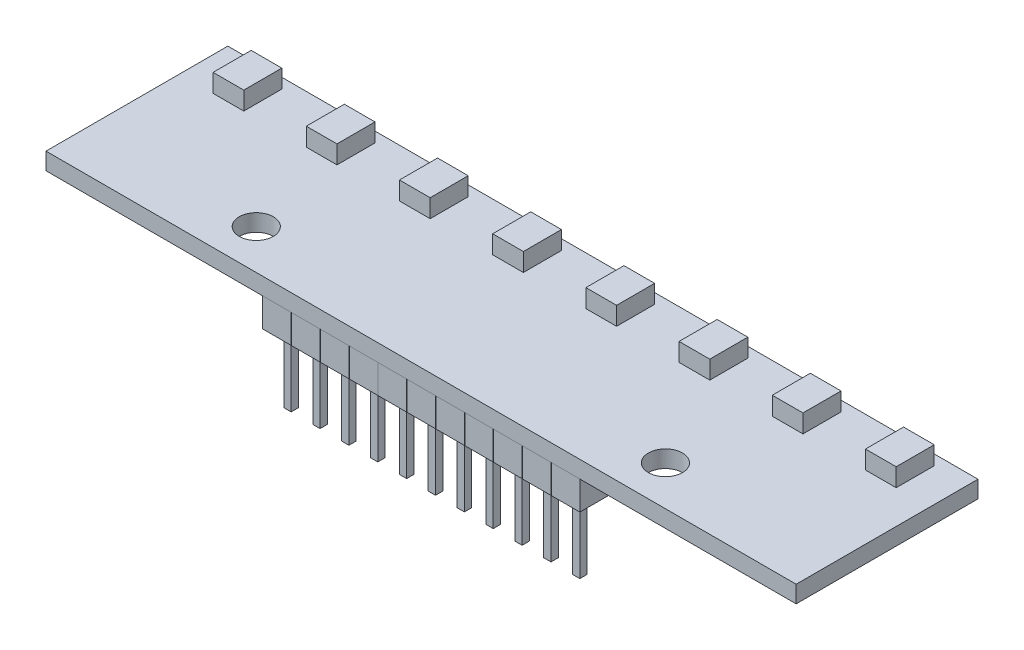
SolidWorks part; units mm, degrees
ref_plane "Front Plane" through (0, 0, 0) normal (0, 0, 1) x (1, 0, 0)
ref_plane "Top Plane" through (0, 0, 0) normal (0, 1, 0) x (1, 0, 0)
ref_plane "Right Plane" through (0, 0, 0) normal (1, 0, 0) x (0, 0, -1)
sketch "Sketch1" plane through (0, 0, 0) normal (0, 1, 0) x (1, 0, 0)
  line L0 (-18, -4.5) -> (18, -4.5) construction
  line L1 (-33, -8) -> (33, -8)
  line L2 (-33, -8) -> (-33, 8)
  line L3 (-33, 8) -> (33, 8)
  line L4 (33, -8) -> (33, 8)
  line L5 (-33, -8) -> (33, 8) construction
  line L6 (-33, 8) -> (33, -8) construction
  circle A0 centre (-18, -4.5) radius 1.5
  circle A1 centre (18, -4.5) radius 1.5
  point P0 (0, 0)
  point P10 (0, -4.5)
  dimension "D3" = 3
  dimension "D1" = 66
  dimension "D2" = 16
  dimension "D4" = 36
  dimension "D5" = 3.5
extrude "Boss-Extrude1" add sketch "Sketch1" against normal blind 1.5
sketch "Sketch2" plane through (0, -1.5, 0) normal (0, -1, 0) x (1, 0, 0)
  line L1 (-1.25, 7.98) -> (1.25, 7.98)
  line L3 (-1.25, 5.48) -> (1.25, 5.48)
  line L4 (1.25, 7.98) -> (1.25, 5.48)
  line L5 (-1.25, 7.98) -> (1.25, 5.48) construction
  line L6 (-1.25, 5.48) -> (1.25, 7.98) construction
  line L7 (-33, 8) -> (33, 8) construction
  line L11 (-1.25, 5.48) -> (-1.25, 7.98)
  point P4 (0, 6.73)
  point P6 (0, 5.48)
  dimension "D1" = 2.5
  dimension "D2" = 1.27
extrude "Boss-Extrude2" add sketch "Sketch2" along normal blind 2.54
sketch "Sketch3" plane through (0, -4.04, 0) normal (0, -1, 0) x (-1, 0, 0)
  line L0 (-1.25, -5.48) -> (-1.25, -7.98) construction
  line L1 (0.32, -6.41) -> (-0.32, -6.41)
  line L2 (0.32, -6.41) -> (0.32, -7.05)
  line L3 (0.32, -7.05) -> (-0.32, -7.05)
  line L4 (-0.32, -6.41) -> (-0.32, -7.05)
  line L5 (0.32, -6.41) -> (-0.32, -7.05) construction
  line L6 (0.32, -7.05) -> (-0.32, -6.41) construction
  point P0 (0, -6.73)
  point P10 (-1.25, -6.73)
  dimension "D1" = 0.64
extrude "Boss-Extrude3" add sketch "Sketch3" along normal blind 6
pattern_linear "LPattern1" count 6 spacing 2.54 along (-1, 0, 0) count 6 spacing 2.54 along (1, 0, 0) of "Boss-Extrude2", "Boss-Extrude3"
sketch "Sketch4" plane through (0, 0, 0) normal (0, 1, 0) x (1, 0, 0)
  line L0 (33, 8) -> (-33, 8) construction
  line L1 (-5.45, 7.1) -> (-2.75, 7.1)
  line L2 (-5.45, 7.1) -> (-5.45, 3.75)
  line L3 (-5.45, 3.75) -> (-2.75, 3.75)
  line L4 (-2.75, 7.1) -> (-2.75, 3.75)
  line L5 (2.75, 7.1) -> (5.45, 7.1)
  line L6 (2.75, 7.1) -> (2.75, 3.75)
  line L7 (2.75, 3.75) -> (5.45, 3.75)
  line L8 (5.45, 7.1) -> (5.45, 3.75)
  line L9 (10.95, 7.1) -> (13.65, 7.1)
  line L10 (10.95, 7.1) -> (10.95, 3.75)
  line L11 (10.95, 3.75) -> (13.65, 3.75)
  line L12 (13.65, 7.1) -> (13.65, 3.75)
  line L13 (19.15, 7.1) -> (21.85, 7.1)
  line L14 (19.15, 7.1) -> (19.15, 3.75)
  line L15 (19.15, 3.75) -> (21.85, 3.75)
  line L16 (21.85, 7.1) -> (21.85, 3.75)
  line L17 (27.35, 7.1) -> (30.05, 7.1)
  line L18 (27.35, 7.1) -> (27.35, 3.75)
  line L19 (27.35, 3.75) -> (30.05, 3.75)
  line L20 (30.05, 7.1) -> (30.05, 3.75)
  line L21 (-13.65, 7.1) -> (-10.95, 7.1)
  line L22 (-13.65, 7.1) -> (-13.65, 3.75)
  line L23 (-13.65, 3.75) -> (-10.95, 3.75)
  line L24 (-10.95, 7.1) -> (-10.95, 3.75)
  line L25 (-30.05, 7.1) -> (-27.35, 7.1)
  line L26 (-30.05, 7.1) -> (-30.05, 3.75)
  line L27 (-30.05, 3.75) -> (-27.35, 3.75)
  line L28 (-27.35, 7.1) -> (-27.35, 3.75)
  line L29 (-21.85, 3.75) -> (-19.15, 3.75)
  line L30 (-21.85, 3.75) -> (-21.85, 7.1)
  line L31 (-21.85, 7.1) -> (-19.15, 7.1)
  line L32 (-19.15, 3.75) -> (-19.15, 7.1)
  dimension "D1" = 2.7
  dimension "D2" = 5.5
  dimension "D3" = 5.5
  dimension "D4" = 3.35
  dimension "D5" = 5.5
  dimension "D6" = 5.5
  dimension "D7" = 5.5
  dimension "D8" = 5.5
  dimension "D9" = 5.5
  dimension "D10" = 2.75
  dimension "D11" = 0.9
extrude "Boss-Extrude4" add sketch "Sketch4" along normal blind 1.6
